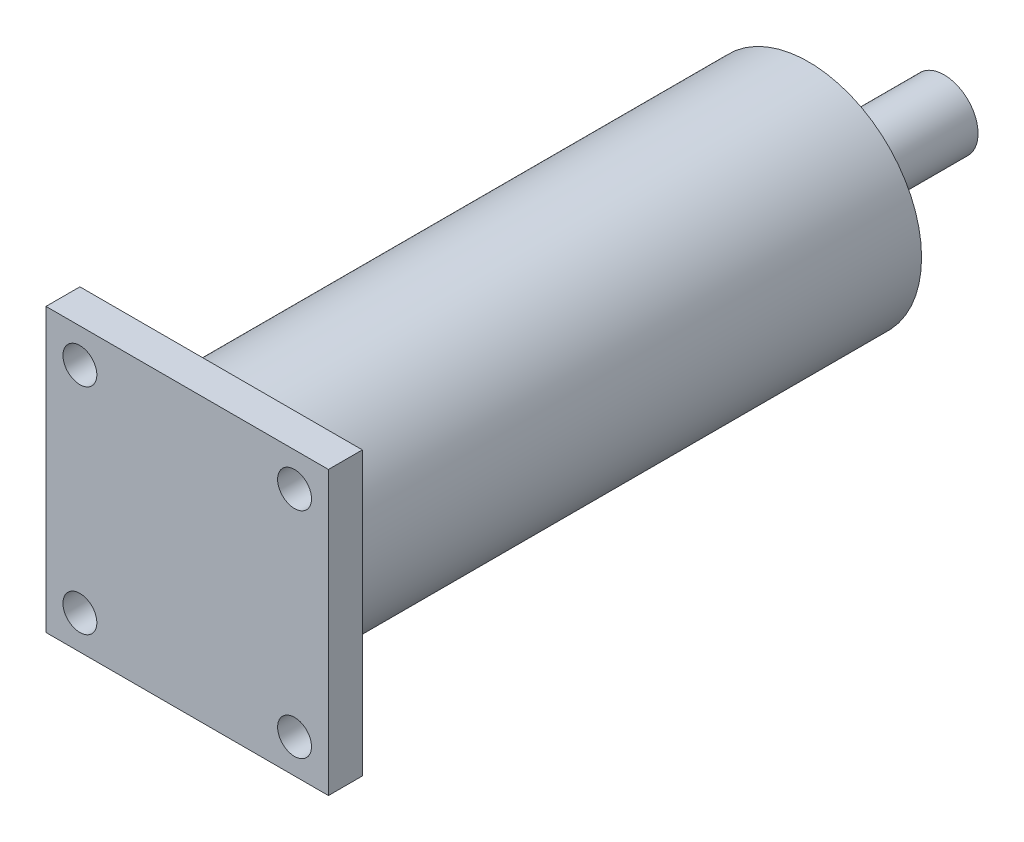
SolidWorks part; units mm, degrees
ref_plane "前视基准面" through (0, 0, 0) normal (0, 0, 1) x (1, 0, 0)
ref_plane "上视基准面" through (0, 0, 0) normal (0, 1, 0) x (1, 0, 0)
ref_plane "右视基准面" through (0, 0, 0) normal (1, 0, 0) x (0, 0, -1)
sketch "草图2" plane through (0, 0, 0) normal (0, 0, 1) x (1, 0, 0)
  line L1 (0, 0) -> (25, 0)
  line L2 (0, 0) -> (0, -25)
  line L3 (0, -25) -> (25, -25)
  line L4 (25, 0) -> (25, -25)
  dimension "D1" = 25
  dimension "D2" = 25
extrude "凸台-拉伸1" add sketch "草图2" along normal blind 3
sketch "草图3" plane through (0, 0, 0) normal (0, 0, -1) x (-1, 0, 0)
  line L0 (-12.5, 0) -> (-12.5, -16.674) construction
  line L1 (-25, 0) -> (0, 0) construction
  line L2 (-25, -12.5) -> (0, -12.5) construction
  line L3 (-25, -25) -> (-25, 0) construction
  line L4 (0, 0) -> (0, -25) construction
  circle A0 centre (-22, -3) radius 1.5
  circle A1 centre (-3, -3) radius 1.5
  circle A2 centre (-3, -22) radius 1.5
  circle A3 centre (-22, -22) radius 1.5
  dimension "D3" = 3
  dimension "D1" = 3
  dimension "D2" = 3
extrude "切除-拉伸2" cut sketch "草图3" against normal through all
sketch "草图4" plane through (0, 0, 3) normal (0, 0, 1) x (1, 0, 0)
  line L0 (0, 0) -> (25, -25) construction
  line L7 (19, -19) -> (6, -6) construction
  circle A0 centre (12.5, -12.5) radius 10
  point P4 (12.5, -12.5)
  dimension "D1" = 20
extrude "凸台-拉伸2" add sketch "草图4" against normal blind 52 from surface at -3 starting at face at (23.5, -22, 0)
sketch "草图5" plane through (0, 0, -52) normal (0, 0, -1) x (-1, 0, 0)
  line L0 (-21.2215, -17.3924) -> (-3.7785, -7.6076) construction
  circle A3 centre (-12.5, -12.5) radius 10 construction
  circle A4 centre (-12.5, -12.5) radius 3
  dimension "D1" = 6
extrude "凸台-拉伸3" add sketch "草图5" along normal blind 12
